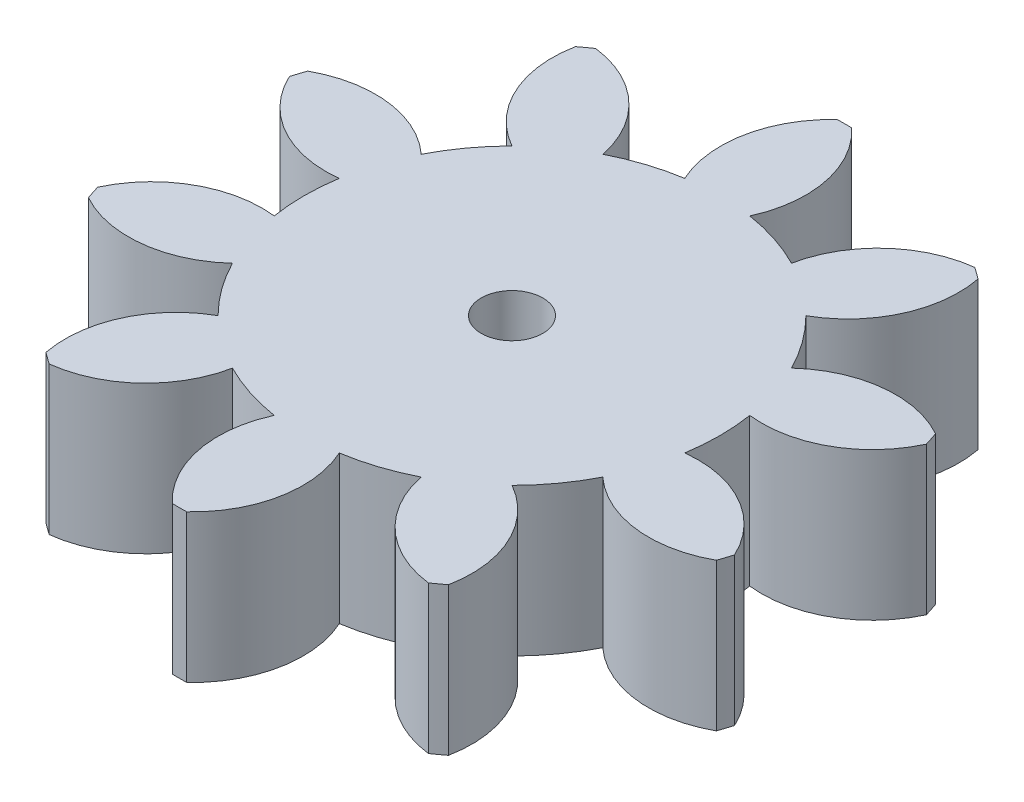
SolidWorks part; units mm, degrees
ref_plane "Front Plane" through (0, 0, 0) normal (0, 0, 1) x (1, 0, 0)
ref_plane "Top Plane" through (0, 0, 0) normal (0, 1, 0) x (1, 0, 0)
ref_plane "Right Plane" through (0, 0, 0) normal (1, 0, 0) x (0, 0, -1)
sketch "Sketch1" plane through (0, 0, 0) normal (0, 1, 0) x (1, 0, 0)
  circle B0 centre (44.5736, 30.0605) radius 2.5
  arc B1 (45.1595, 57.0541) -> (43.9877, 57.0541) centre (44.5736, 30.0605) ccw
  arc B2 (47.2173, 46.7261) -> (45.1595, 57.0541) centre (39.0302, 50.4639) ccw
  arc B3 (52.2306, 45.0972) -> (47.2173, 46.7261) centre (44.5736, 30.0605) ccw
  arc B4 (59.966, 52.2432) -> (52.2306, 45.0972) centre (61.0512, 43.3089) ccw
  arc B5 (60.9141, 51.5544) -> (59.966, 52.2432) centre (44.5736, 30.0605) ccw
  arc B6 (56.5082, 41.9894) -> (60.9141, 51.5544) centre (52.0817, 49.8256) ccw
  arc B7 (59.6066, 37.7247) -> (56.5082, 41.9894) centre (44.5736, 30.0605) ccw
  arc B8 (70.065, 38.9592) -> (59.6066, 37.7247) centre (65.6914, 31.0934) ccw
  arc B9 (70.4271, 37.8447) -> (70.065, 38.9592) centre (44.5736, 30.0605) ccw
  arc B10 (61.2405, 32.6962) -> (70.4271, 37.8447) centre (62.2654, 41.6376) ccw
  arc B11 (61.2405, 27.4248) -> (61.2405, 32.6962) centre (44.5736, 30.0605) ccw
  arc B12 (70.4271, 22.2763) -> (61.2405, 27.4248) centre (62.2654, 18.4834) ccw
  arc B13 (70.065, 21.1617) -> (70.4271, 22.2763) centre (44.5736, 30.0605) ccw
  arc B14 (59.6066, 22.3963) -> (70.065, 21.1617) centre (65.6914, 29.0276) ccw
  arc B15 (56.5082, 18.1316) -> (59.6066, 22.3963) centre (44.5736, 30.0605) ccw
  arc B16 (60.9141, 8.5666) -> (56.5082, 18.1316) centre (52.0817, 10.2954) ccw
  arc B17 (59.966, 7.8778) -> (60.9141, 8.5666) centre (44.5736, 30.0605) ccw
  arc B18 (52.2306, 15.0238) -> (59.966, 7.8778) centre (61.0512, 16.8121) ccw
  arc B19 (47.2173, 13.3949) -> (52.2306, 15.0238) centre (44.5736, 30.0605) ccw
  arc B20 (45.1595, 3.0668) -> (47.2173, 13.3949) centre (39.0302, 9.6571) ccw
  arc B21 (43.9877, 3.0668) -> (45.1595, 3.0668) centre (44.5736, 30.0605) ccw
  arc B22 (41.9299, 13.3949) -> (43.9877, 3.0668) centre (50.117, 9.6571) ccw
  arc B23 (36.9166, 15.0238) -> (41.9299, 13.3949) centre (44.5736, 30.0605) ccw
  arc B24 (29.1812, 7.8778) -> (36.9166, 15.0238) centre (28.096, 16.8121) ccw
  arc B25 (28.2331, 8.5666) -> (29.1812, 7.8778) centre (44.5736, 30.0605) ccw
  arc B26 (32.639, 18.1316) -> (28.2331, 8.5666) centre (37.0655, 10.2954) ccw
  arc B27 (29.5406, 22.3963) -> (32.639, 18.1316) centre (44.5736, 30.0605) ccw
  arc B28 (19.0822, 21.1617) -> (29.5406, 22.3963) centre (23.4558, 29.0276) ccw
  arc B29 (18.7201, 22.2763) -> (19.0822, 21.1617) centre (44.5736, 30.0605) ccw
  arc B30 (27.9067, 27.4248) -> (18.7201, 22.2763) centre (26.8818, 18.4834) ccw
  arc B31 (27.9067, 32.6962) -> (27.9067, 27.4248) centre (44.5736, 30.0605) ccw
  arc B32 (18.7201, 37.8447) -> (27.9067, 32.6962) centre (26.8818, 41.6376) ccw
  arc B33 (19.0822, 38.9592) -> (18.7201, 37.8447) centre (44.5736, 30.0605) ccw
  arc B34 (29.5406, 37.7247) -> (19.0822, 38.9592) centre (23.4558, 31.0934) ccw
  arc B35 (32.639, 41.9894) -> (29.5406, 37.7247) centre (44.5736, 30.0605) ccw
  arc B36 (28.2331, 51.5544) -> (32.639, 41.9894) centre (37.0655, 49.8256) ccw
  arc B37 (29.1812, 52.2432) -> (28.2331, 51.5544) centre (44.5736, 30.0605) ccw
  arc B38 (36.9166, 45.0972) -> (29.1812, 52.2432) centre (28.096, 43.3089) ccw
  arc B39 (41.9299, 46.7261) -> (36.9166, 45.0972) centre (44.5736, 30.0605) ccw
  arc B40 (43.9877, 57.0541) -> (41.9299, 46.7261) centre (50.117, 50.4639) ccw
sketch_block_instance "Block1-1"
sketch_block "Block1"
extrude "Boss-Extrude2" add sketch "Sketch1" along normal blind 12 separate body
